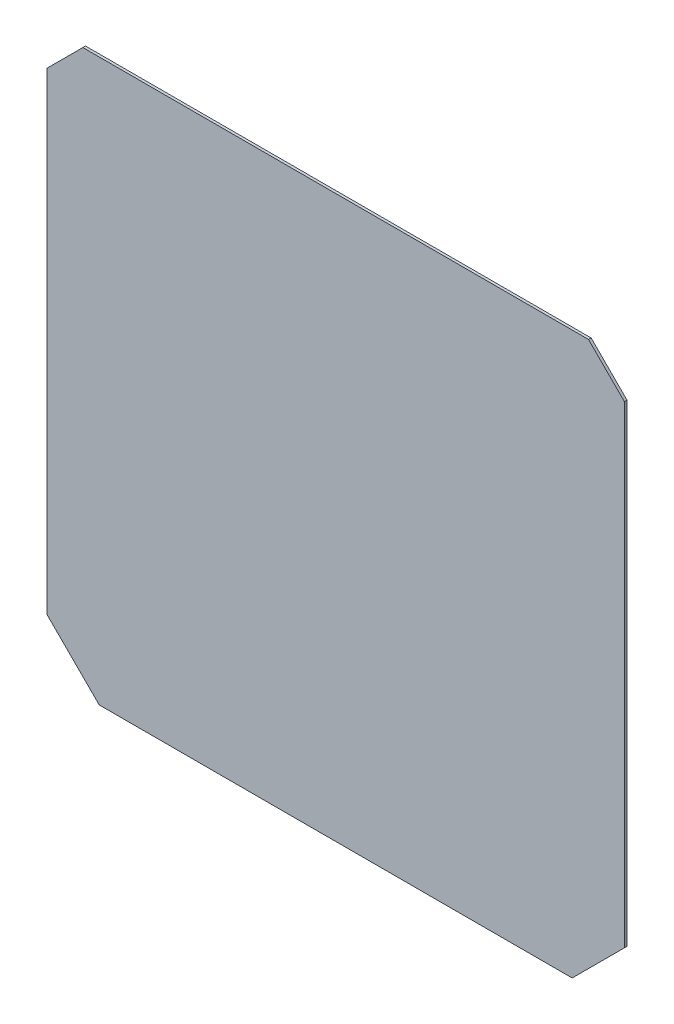
SolidWorks part; units mm, degrees
ref_plane "정면" through (0, 0, 0) normal (0, 0, 1) x (1, 0, 0)
ref_plane "윗면" through (0, 0, 0) normal (0, 1, 0) x (1, 0, 0)
ref_plane "우측면" through (0, 0, 0) normal (1, 0, 0) x (0, 0, -1)
sketch "스케치1" plane through (0, 0, 0) normal (0, 0, 1) x (1, 0, 0)
  line L0 (-221, 181) -> (-181, 221)
  line L1 (-181, 221) -> (181, 221)
  line L2 (-221, 181) -> (-221, -181)
  line L3 (-181, -221) -> (181, -221)
  line L4 (221, 181) -> (221, -181)
  line L5 (-221, 221) -> (221, -221) construction
  line L6 (-221, -221) -> (221, 221) construction
  line L7 (-221, -181) -> (-181, -221)
  line L8 (181, -221) -> (221, -181)
  line L9 (181, 221) -> (221, 181)
  point P4 (0, 0)
  dimension "D1" = 442
  dimension "D2" = 442
extrude "보스-돌출1" add sketch "스케치1" along normal blind 2
sketch "스케치3" plane through (0, 0, 0) normal (0, 0, 1) x (1, 0, 0)
  line L1 (-215, -215) -> (215, -215) construction
  line L2 (-215, -215) -> (-215, 215) construction
  line L3 (-215, 215) -> (215, 215) construction
  line L4 (215, -215) -> (215, 215) construction
  line L5 (-215, -215) -> (215, 215) construction
  line L6 (-215, 215) -> (215, -215) construction
  line L7 (-215, 215) -> (215, 215) construction
  line L8 (-215, 215) -> (-215, 208.5) construction
  line L9 (-215, 208.5) -> (215, 208.5) construction
  line L10 (215, 215) -> (215, 208.5) construction
  line L11 (-215, 215) -> (215, 208.5) construction
  line L12 (-215, 208.5) -> (215, 215) construction
  line L13 (-215, 208.5) -> (225.6956, 208.5)
  line L14 (-215, 208.5) -> (-215, 252.542)
  line L15 (-215, 252.542) -> (225.6956, 252.542)
  line L16 (225.6956, 208.5) -> (225.6956, 252.542)
  line L17 (-215, 208.5) -> (225.6956, 252.542) construction
  line L18 (-215, 252.542) -> (225.6956, 208.5) construction
  point P0 (0, 0)
  point P8 (0, 211.75)
  point P12 (5.3478, 230.521)
  dimension "D1" = 430
  dimension "D2" = 430
  dimension "D3" = 6.5
extrude "컷-돌출1" cut sketch "스케치3" against normal blind 10 and the other way blind 10 contours L14 L15 L16 L13
